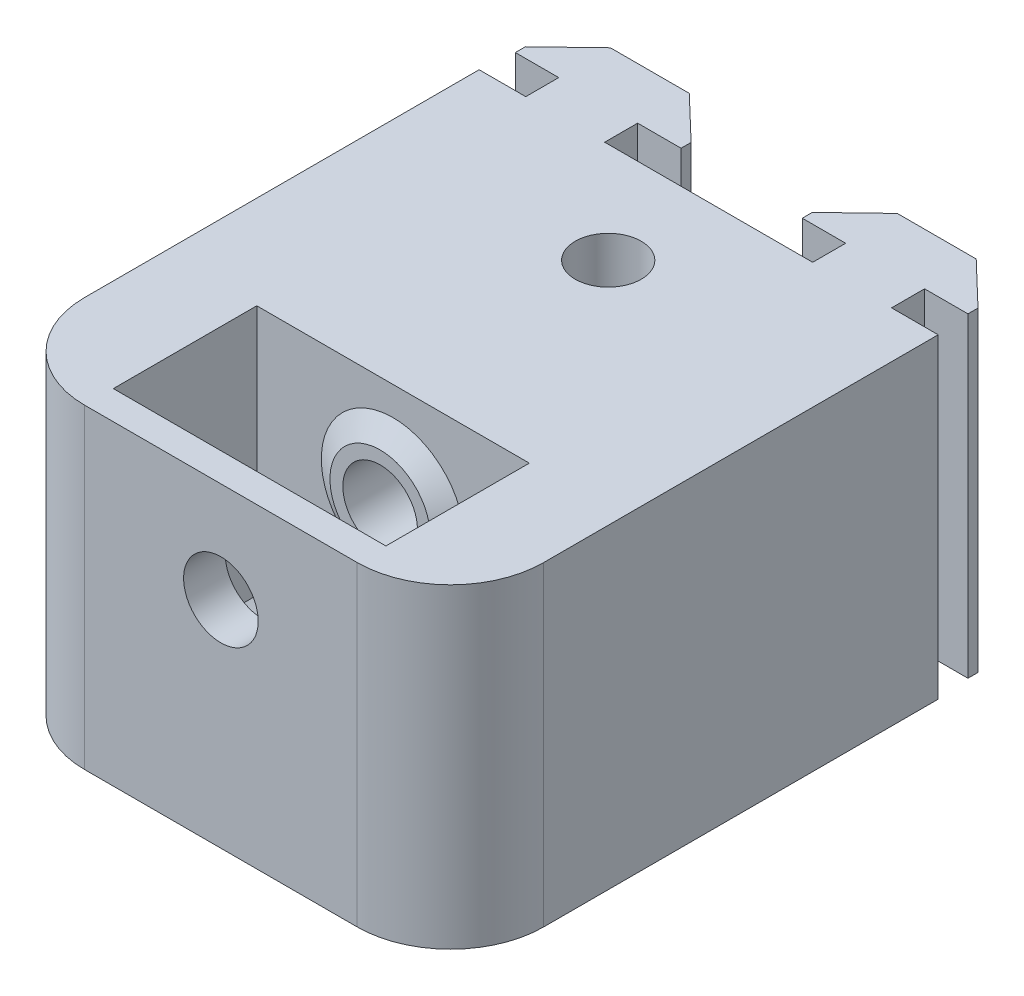
SolidWorks part; units mm, degrees
material "ABS"
ref_plane "Front Plane" through (0, 0, 0) normal (0, 0, 1) x (1, 0, 0)
ref_plane "Top Plane" through (0, 0, 0) normal (0, 1, 0) x (1, 0, 0)
ref_plane "Right Plane" through (0, 0, 0) normal (1, 0, 0) x (0, 0, -1)
sketch "Sketch1" plane through (0, 0, 0) normal (0, 1, 0) x (1, 0, 0)
  line L0 (-32, 0) -> (-32, -27.5)
  line L1 (-25.5, -34) -> (-6.5, -34)
  line L2 (0, -27.5) -> (0, 0)
  line L3 (-32, 0) -> (-28.75, 0)
  line L4 (-25.5, -22) -> (-32, -22) construction
  line L5 (-6.5, -22) -> (0, -22) construction
  line L12 (-3.25, 0) -> (-3.25, 2.3)
  line L13 (-3.25, 2.3) -> (-0.225, 2.3)
  line L14 (-0.225, 2.3) -> (-0.225, 3)
  line L15 (-0.225, 3) -> (-3.25, 5.9)
  line L16 (-3.25, 5.9) -> (-8.75, 5.9)
  line L17 (-8.75, 5.9) -> (-11.775, 3)
  line L18 (-11.775, 3) -> (-11.775, 2.3)
  line L19 (-11.775, 2.3) -> (-8.75, 2.3)
  line L20 (-8.75, 2.3) -> (-8.75, 0)
  line L21 (-3.25, 0) -> (0, 0)
  line L22 (-23.25, 0) -> (-23.25, 2.3)
  line L23 (-23.25, 2.3) -> (-20.225, 2.3)
  line L24 (-20.225, 2.3) -> (-20.225, 3)
  line L25 (-20.225, 3) -> (-23.25, 5.9)
  line L26 (-23.25, 5.9) -> (-28.75, 5.9)
  line L27 (-28.75, 5.9) -> (-31.775, 3)
  line L28 (-31.775, 3) -> (-31.775, 2.3)
  line L29 (-31.775, 2.3) -> (-28.75, 2.3)
  line L30 (-28.75, 2.3) -> (-28.75, 0)
  line L31 (-23.25, 0) -> (-8.75, 0)
  line L32 (-28.75, 0) -> (-23.25, 0) construction
  line L33 (-8.75, 0) -> (-3.25, 0) construction
  line L34 (-26, 0) -> (-26, 5.9) construction
  line L35 (-6, 0) -> (-6, 5.9) construction
  line L36 (-25.5, -22) -> (-6.5, -22)
  line L37 (-6.5, -22) -> (-6.5, -32)
  line L38 (-6.5, -32) -> (-25.5, -32)
  line L39 (-25.5, -32) -> (-25.5, -22)
  line L41 (-16, 0) -> (-16, -7) construction
  arc A0 (-32, -27.5) -> (-25.5, -34) centre (-25.5, -27.5) ccw
  arc A1 (-6.5, -34) -> (0, -27.5) centre (-6.5, -27.5) ccw
  circle A2 centre (-16, -7) radius 2.3
  dimension "D2" = 19
  dimension "D3" = 2
  dimension "D12" = 22
  dimension "D14" = 4.6
  dimension "D15" = 13
  dimension "D4" = 32
  dimension "D5" = 2.3
  dimension "D6" = 5.9
  dimension "D7" = 11.55
  dimension "D8" = 20
  dimension "D9" = 0.7
  dimension "D10" = 5.5
  dimension "D11" = 10
  dimension "D13" = 7
extrude "Boss-Extrude1" add sketch "Sketch1" along normal blind 22
sketch "Sketch2" plane through (0, 0, 32) normal (0, 0, -1) x (-1, 0, 0)
  line L0 (16, 22) -> (16, 15) construction
  line L1 (25.5, 22) -> (6.5, 22) construction
  line L2 (21.5, 0) -> (21.5, 8.5193)
  line L4 (10.5, 0) -> (10.5, 8.5193)
  line L5 (21.5, 0) -> (10.5, 0)
  line L6 (25.5, 0) -> (21.5, 0) construction
  line L7 (6.5, 0) -> (10.5, 0) construction
  arc A0 (10.5, 8.5193) -> (21.5, 8.5193) centre (16, 15) ccw
  dimension "D2" = 17
  dimension "D1" = 7
  dimension "D3" = 11
extrude "Boss-Extrude2" add sketch "Sketch2" along normal up to next
ref_plane "Plane1" through (-16, 0, 0) normal (1, 0, 0) x (0, 0, -1)
sketch "Sketch4" plane through (-16, 0, 0) normal (1, 0, 0) x (0, 0, -1)
  line L0 (-32, 20) -> (-31.1, 18.5)
  line L1 (-32, 22) -> (-32, 0) construction
  line L2 (-31.1, 18.5) -> (-31.1, 15)
  line L3 (-31.1, 15) -> (-32, 15)
  line L4 (-32, 15) -> (-32, 20)
  line L5 (-27.5, 22) -> (-34, 22) construction
  line L6 (-32, 15) -> (-25.2886, 15) construction
  line L7 (-22, 15) -> (-22.9, 15)
  line L8 (-22, 22) -> (-22, 0) construction
  line L9 (-22.9, 15) -> (-22.9, 18.5)
  line L10 (-22.9, 18.5) -> (-22, 20)
  line L11 (-22, 20) -> (-22, 15)
  dimension "D1" = 7
  dimension "D2" = 5
  dimension "D3" = 3.5
  dimension "D4" = 0.9
revolve "Revolve1" add sketch "Sketch4" angle 360 about L6
sketch "Sketch5" plane through (0, 0, 34) normal (0, 0, 1) x (1, 0, 0)
  line L0 (-16, 22) -> (-16, 15) construction
  line L1 (-25.5, 22) -> (-6.5, 22) construction
  circle A0 centre (-16, 15) radius 2.6
  dimension "D2" = 5.2
  dimension "D1" = 7
extrude "Cut-Extrude1" cut sketch "Sketch5" against normal blind 17.5
